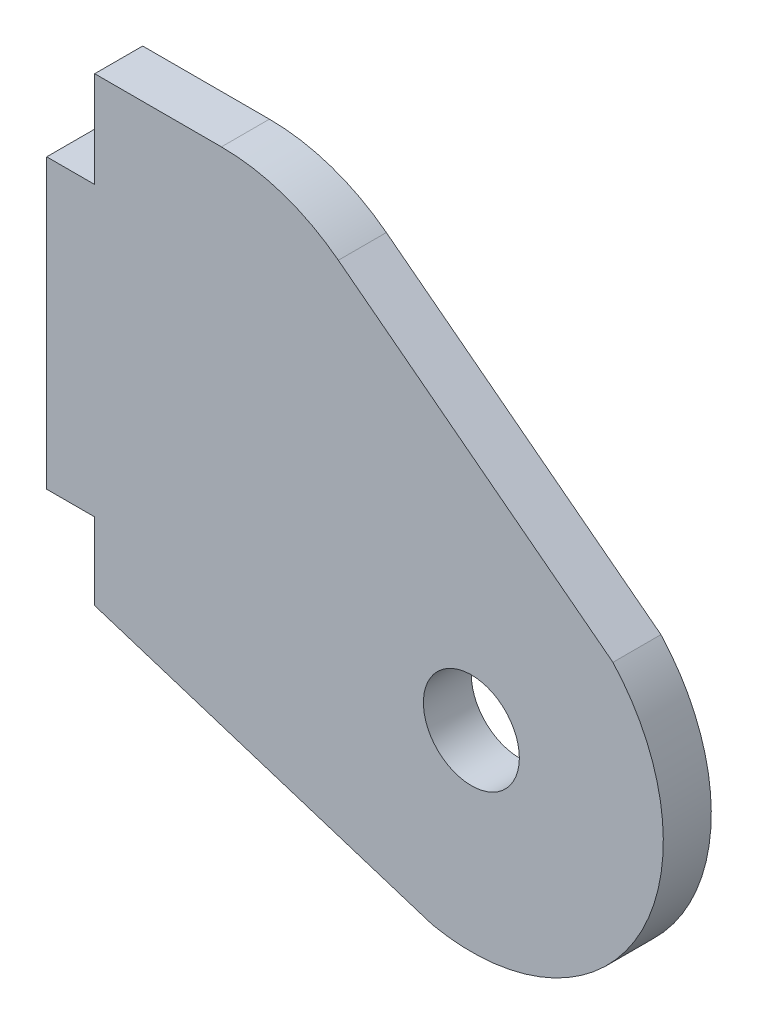
SolidWorks part; units mm, degrees
material "AISI 4340 Steel, annealed"
ref_plane "X-Y Datum" through (0, 0, 0) normal (0, 0, 1) x (1, 0, 0)
ref_plane "X-Z Datum" through (0, 0, 0) normal (0, 1, 0) x (1, 0, 0)
ref_plane "Y-Z Datum" through (0, 0, 0) normal (1, 0, 0) x (0, 0, -1)
sketch "Sketch1" plane through (0, 0, 0) normal (0, 0, 1) x (1, 0, 0)
  line L0 (-26.2895, -31.4818) -> (-29.4645, -31.4818)
  line L1 (-26.2895, -6.0818) -> (-13.5895, -6.0818)
  line L2 (-26.2895, -6.0818) -> (-26.2895, -12.4318)
  line L5 (-29.4645, -31.4818) -> (-29.4645, -12.4318)
  line L6 (-26.2895, -36.5618) -> (-3.9375, -43.68)
  line L7 (-13.5895, -6.0818) -> (8.0005, -22.6662)
  line L8 (-29.4645, -12.4318) -> (-26.2895, -12.4318)
  line L9 (-26.2895, -31.4818) -> (-26.2895, -36.5618)
  arc A0 (8.0005, -22.6662) -> (-3.9375, -43.68) centre (-1.3658, -31.2431) cw
  point P10 (-26.2895, -30.8922)
  dimension "D2" = 12.7
  dimension "D1" = 30.48
  dimension "D3" = 12.7
  dimension "D4" = 22.352
  dimension "D5" = 34.29
  dimension "D6" = 3.175
  dimension "D7" = 19.05
  dimension "D8" = 6.35
extrude "Boss-Extrude1" add sketch "Sketch1" along normal blind 3.175
hole_wizard "1/4 (0.25) Diameter Hole1" positions "Sketch2" profile "Sketch3" hole size "1/4" standard "ANSI Inch"
sketch "Sketch2" plane through (0, 0, 3.175) normal (0, 0, 1) x (1, 0, 0)
  point P0 (-1.3658, -31.2431)
sketch "Sketch3" plane through (-1.3658, -31.2431, 3.175) normal (1, 0, 0) x (0, -1, 0)
  line L0 (0, 0) -> (0, 11.176)
  line L1 (0, 11.176) -> (3.175, 9.2683)
  line L2 (3.175, 9.2683) -> (3.175, 0)
  line L5 (3.175, 0) -> (0, 0)
  line L10 (0, 11.176) -> (-3.175, 9.2683) construction
  line L11 (0, -6.35) -> (0, 107.95) construction
  dimension "Hole Dia." = 6.35
  dimension "Hole Depth" = 11.176
  dimension "Drill Angle" = 118
fillet "Fillet1" radius 12.7 1 edges at (-13.5895, -6.0818, 1.5875)
